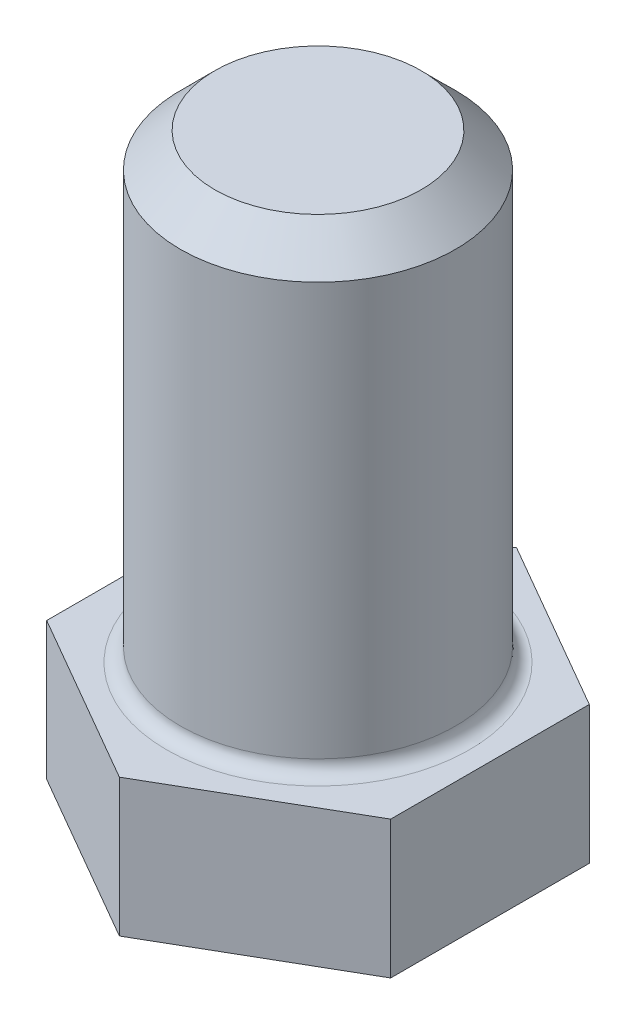
SolidWorks part; units mm, degrees
ref_plane "Front Plane" through (0, 0, 0) normal (0, 0, 1) x (1, 0, 0)
ref_plane "Top Plane" through (0, 0, 0) normal (0, 1, 0) x (1, 0, 0)
ref_plane "Right Plane" through (0, 0, 0) normal (1, 0, 0) x (0, 0, -1)
sketch "Sketch1" plane through (0, 0, 0) normal (0, 1, 0) x (1, 0, 0)
  line L1 (0, 2.8868) -> (-2.5, 1.4434)
  line L2 (-2.5, 1.4434) -> (-2.5, -1.4434)
  line L3 (-2.5, -1.4434) -> (0, -2.8868)
  line L4 (0, -2.8868) -> (2.5, -1.4434)
  line L5 (2.5, -1.4434) -> (2.5, 1.4434)
  line L6 (2.5, 1.4434) -> (0, 2.8868)
  circle A0 centre (0, 0) radius 2.5 construction
  dimension "D1" = 5
extrude "Boss-Extrude1" add sketch "Sketch1" along normal blind 2
sketch "Sketch2" plane through (0, 2, 0) normal (0, 1, 0) x (1, 0, 0)
  circle A0 centre (0, 0) radius 2
  dimension "D1" = 4
extrude "Boss-Extrude2" add sketch "Sketch2" along normal blind 6.7
chamfer "Chamfer1" distance 0.5 angle 45 1 edges at (0, 8.7, 2)
fillet "Fillet1" radius 0.2 1 edges at (0, 2, 2)
